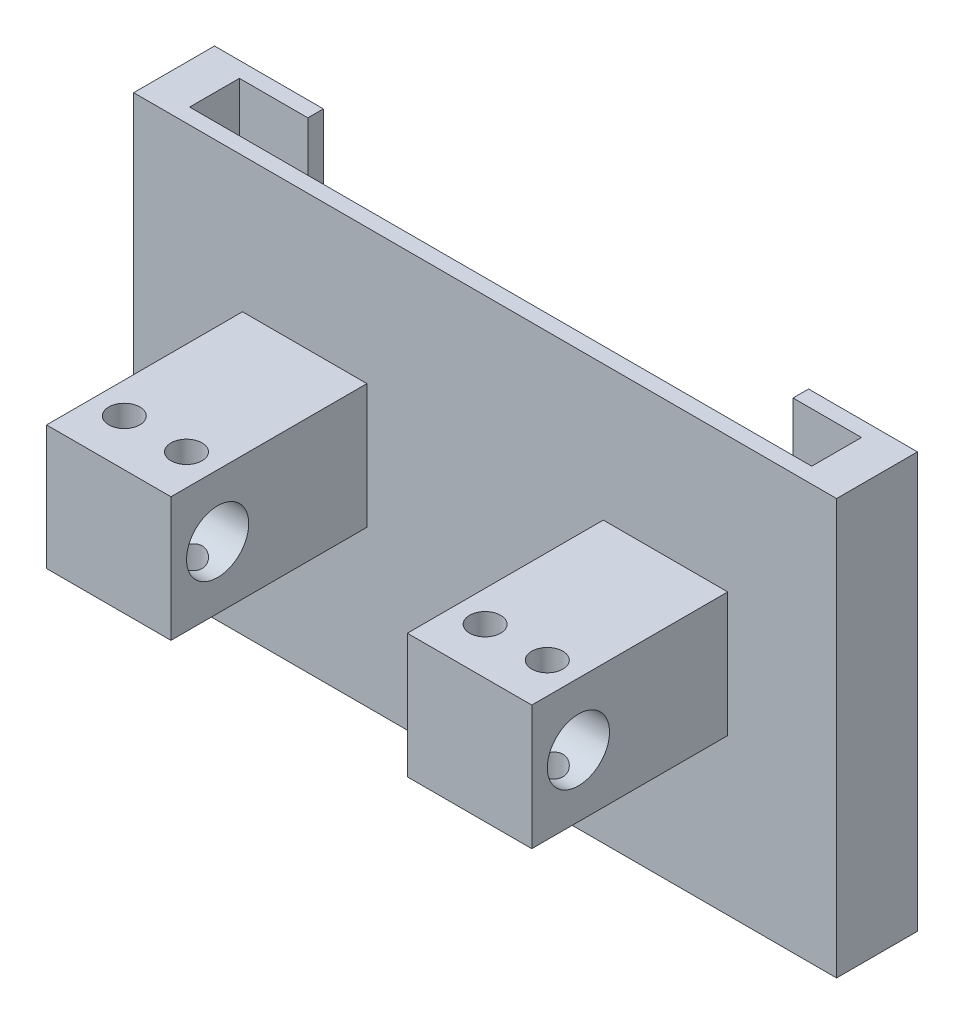
SolidWorks part; units mm, degrees
material "PVC Rigid"
ref_plane "Front Plane" through (0, 0, 0) normal (0, 0, 1) x (1, 0, 0)
ref_plane "Top Plane" through (0, 0, 0) normal (0, 1, 0) x (1, 0, 0)
ref_plane "Right Plane" through (0, 0, 0) normal (1, 0, 0) x (0, 0, -1)
sketch "Sketch3" plane through (0, 0, 0) normal (0, 0, 1) x (1, 0, 0)
  line L0 (-113, 63.5) -> (113, 63.5)
  line L1 (113, -70) -> (-113, -70)
  line L2 (113, -70) -> (113, 63.5)
  line L4 (-113, -70) -> (-113, 63.5)
  point P0 (0, 0)
extrude "Boss-Extrude1" add sketch "Sketch3" along normal blind 26 contours L2 L0 L4 L1
sketch "Sketch4" plane through (0, 0, 0) normal (0, 1, 0) x (1, 0, 0)
  line L1 (100, -5) -> (-100, -5)
  line L2 (100, -5) -> (100, -21)
  line L3 (100, -21) -> (-100, -21)
  line L4 (-100, -5) -> (-100, -21)
extrude "Cut-Extrude2" cut sketch "Sketch4" along normal through all and the other way offset from surface (60 mm away) 10 contours L1 L4 L3 L2 other way up to face at (0, -70, 13)
sketch "Sketch6" plane through (0, 0, 26) normal (0, 0, 1) x (1, 0, 0)
  line L1 (-78, 20) -> (-38, 20)
  line L2 (-78, 20) -> (-78, -20)
  line L3 (-78, -20) -> (-38, -20)
  line L4 (0, 0) -> (0, 20) construction
  line L5 (38, 20) -> (38, -20)
  line L6 (78, -20) -> (38, -20)
  line L7 (78, 20) -> (78, -20)
  line L8 (78, 20) -> (38, 20)
  line L9 (-38, 20) -> (-38, -20)
  point P0 (0, 0)
  point P8 (0, 0)
extrude "Boss-Extrude5" add sketch "Sketch6" along normal blind 63
sketch "Sketch7" plane through (113, 0, 0) normal (1, 0, 0) x (0, 0, -1)
  circle A0 centre (-74, 0) radius 10
extrude "Cut-Extrude3" cut sketch "Sketch7" against normal blind 260
sketch "Sketch10" plane through (0, 0, 0) normal (0, 0, -1) x (-1, 0, 0)
  line L0 (113, 63.5) -> (-113, 63.5) construction
  line L1 (-78, 63.5) -> (78, 63.5)
  line L2 (-78, 63.5) -> (-78, -40)
  line L3 (-78, -40) -> (78, -40)
  line L4 (78, 63.5) -> (78, -40)
sketch "Sketch13" plane through (0, 20, 0) normal (0, 1, 0) x (1, 0, 0)
  line L0 (0, 0) -> (0, -174.6231) construction
  circle A0 centre (-68, -74) radius 5
  circle A1 centre (-48, -74) radius 5
  circle A2 centre (48, -74) radius 5
  circle A3 centre (68, -74) radius 5
  dimension "D1" = 2
extrude "Cut-Extrude6" cut sketch "Sketch13" against normal through all
extrude "Cut-Extrude5" cut sketch "Sketch10" against normal up to surface (5 mm away) contours L2 L3 L4 L1 up to face at (0, 1.75, 5)
